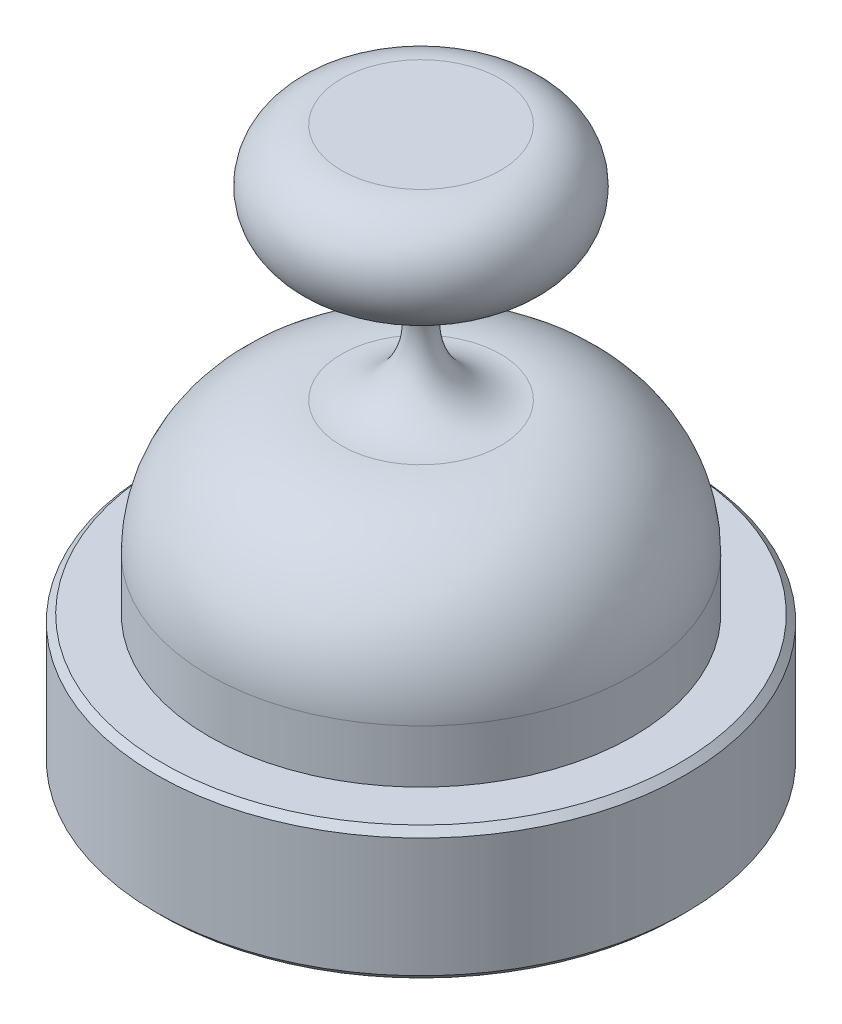
SolidWorks part; units mm, degrees
ref_plane "Face" through (0, 0, 0) normal (0, 0, 1) x (1, 0, 0)
ref_plane "Dessus" through (0, 0, 0) normal (0, 1, 0) x (1, 0, 0)
ref_plane "Droite" through (0, 0, 0) normal (1, 0, 0) x (0, 0, -1)
sketch "Esquisse1" plane through (0, 0, 0) normal (0, 0, 1) x (1, 0, 0)
  line L0 (0, 0) -> (0, 180) construction
  line L1 (0, 0) -> (-80, 0) construction
  line L2 (0, 160) -> (-30, 160)
  line L3 (-80, 0) -> (-80, 20)
  line L4 (-30, 160) -> (-30, 0) construction
  line L5 (-80, 0) -> (0, 0)
  line L6 (0, 160) -> (0, 0)
  arc A0 (-30, 160) -> (-30, 120) centre (-30, 140) ccw
  arc A1 (-30, 120) -> (-30, 70) centre (-30, 95) cw
  arc A2 (-80, 20) -> (-30, 70) centre (-30, 20) cw
  point P3 (0, 160)
  dimension "D5" = 20
  dimension "D6" = 20
  dimension "D1" = 180
  dimension "D2" = 80
  dimension "D3" = 20
  dimension "D4" = 30
revolve "Révolution2" add sketch "Esquisse1" angle 360 about L6
sketch "Esquisse2" plane through (0, 0, 0) normal (0, -1, 0) x (1, 0, 0)
  circle A0 centre (0, 0) radius 100
  dimension "D1" = 200
extrude "Extrusion1" add sketch "Esquisse2" along normal blind 50
chamfer "Chanfrein1" distance 2.5 angle 45 2 edges at (0, -50, -100) (0, 0, -100)
